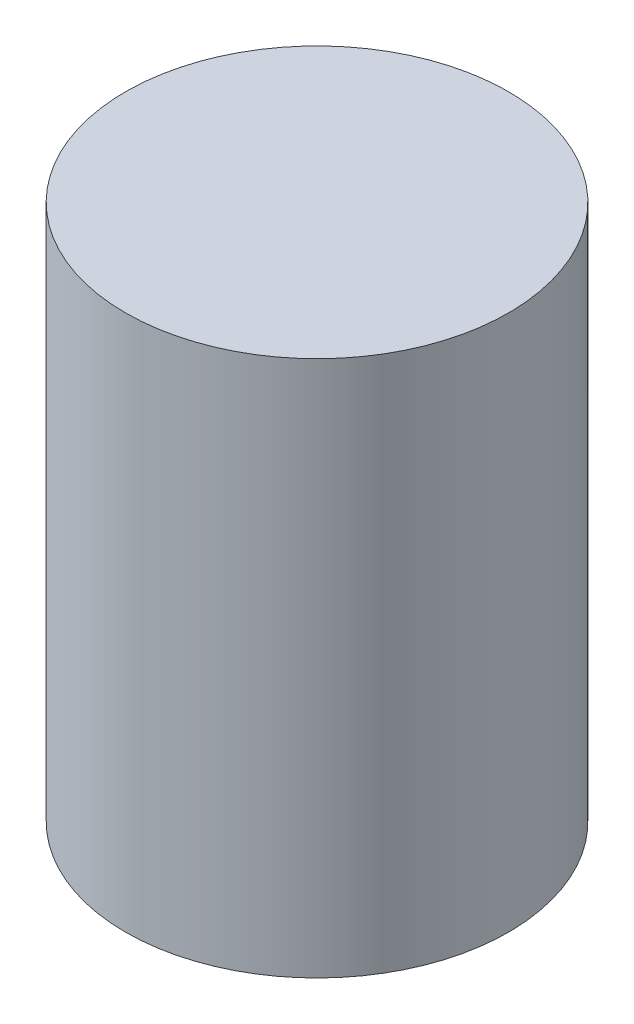
SolidWorks part; units mm, degrees
ref_plane "Front" through (0, 0, 0) normal (0, 0, 1) x (1, 0, 0)
ref_plane "Top" through (0, 0, 0) normal (0, 1, 0) x (1, 0, 0)
ref_plane "Right" through (0, 0, 0) normal (1, 0, 0) x (0, 0, -1)
sketch "Sketch1" plane through (0, 0, 0) normal (0, 1, 0) x (1, 0, 0)
  circle A0 centre (0, 0) radius 50
  dimension "D1" = 100
extrude "Boss-Extrude1" add sketch "Sketch1" along normal blind 140
sketch "Sketch3" plane through (0, 0, 0) normal (0, -1, 0) x (1, 0, 0)
  circle A0 centre (0, 0) radius 10
  dimension "D1" = 20
extrude "Cut-Extrude2" cut sketch "Sketch3" against normal blind 120
sketch "Sketch4" plane through (0, 0, 0) normal (0, -1, 0) x (1, 0, 0)
  circle A0 centre (0, 0) radius 30
  dimension "D1" = 60
extrude "Cut-Extrude3" cut sketch "Sketch4" against normal blind 40
